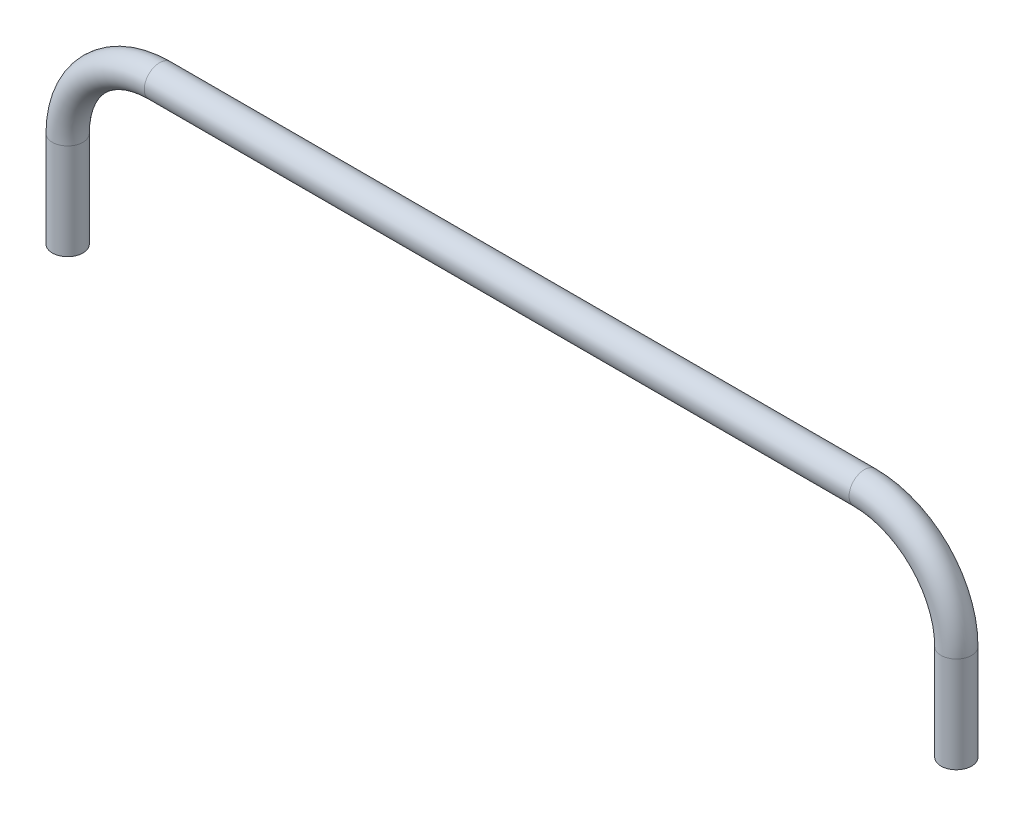
SolidWorks part; units mm, degrees
material "Cast Carbon Steel"
ref_plane "Front Plane" through (0, 0, 0) normal (0, 0, 1) x (1, 0, 0)
ref_plane "Top Plane" through (0, 0, 0) normal (0, 1, 0) x (1, 0, 0)
ref_plane "Right Plane" through (0, 0, 0) normal (1, 0, 0) x (0, 0, -1)
sketch "Sketch1" plane through (0, 0, 0) normal (0, 0, 1) x (1, 0, 0)
  line L0 (0, 0) -> (0, 79.502)
  line L1 (76.2, 155.702) -> (660.4, 155.702)
  line L2 (736.6, 79.502) -> (736.6, 0)
  arc A0 (736.6, 79.502) -> (660.4, 155.702) centre (660.4, 79.502) ccw
  arc A1 (0, 79.502) -> (76.2, 155.702) centre (76.2, 79.502) cw
  dimension "D2" = 76.2
  dimension "D1" = 736.6
  dimension "D3" = 79.502
sketch "Sketch14" plane through (0, 0, 0) normal (0, 1, 0) x (1, 0, 0)
  circle A0 centre (0, 0) radius 12.7
  circle A1 centre (0, 0) radius 8.7312
  dimension "D1" = 25.4
  dimension "D2" = 17.4625
sweep "Sweep2" add profiles "Sketch14" path "Sketch1"
